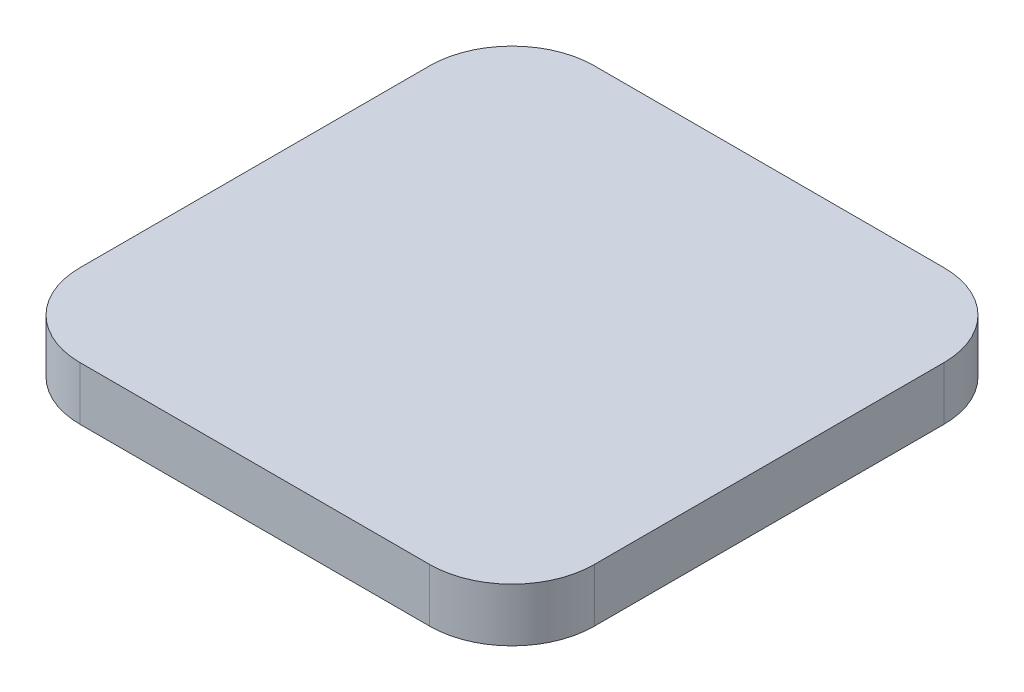
SolidWorks part; units mm, degrees
ref_plane "Front Plane" through (0, 0, 0) normal (0, 0, 1) x (1, 0, 0)
ref_plane "Top Plane" through (0, 0, 0) normal (0, 1, 0) x (1, 0, 0)
ref_plane "Right Plane" through (0, 0, 0) normal (1, 0, 0) x (0, 0, -1)
sketch "Sketch1" plane through (0, 0, 0) normal (0, 1, 0) x (1, 0, 0)
  line L1 (-12.5, -12.5) -> (12.5, -12.5)
  line L2 (-12.5, -12.5) -> (-12.5, 12.5)
  line L3 (-12.5, 12.5) -> (12.5, 12.5)
  line L4 (12.5, -12.5) -> (12.5, 12.5)
  line L5 (-12.5, -12.5) -> (12.5, 12.5) construction
  line L6 (-12.5, 12.5) -> (12.5, -12.5) construction
  point P0 (0, 0)
  dimension "D1" = 25
  dimension "D2" = 25
extrude "Boss-Extrude1" add sketch "Sketch1" along normal blind 2.6
fillet "Fillet1" radius 4 4 edges at (12.5, 1.3, -12.5) (12.5, 1.3, 12.5) (-12.5, 1.3, -12.5) (-12.5, 1.3, 12.5)
sketch "Sketch2" plane through (0, 0, 0) normal (0, -1, 0) x (1, 0, 0)
  circle A0 centre (0, -2.5) radius 0.4
  dimension "D1" = 0.8
  dimension "D2" = 2.5
extrude "Boss-Extrude2" add sketch "Sketch2" along normal blind 1.9
